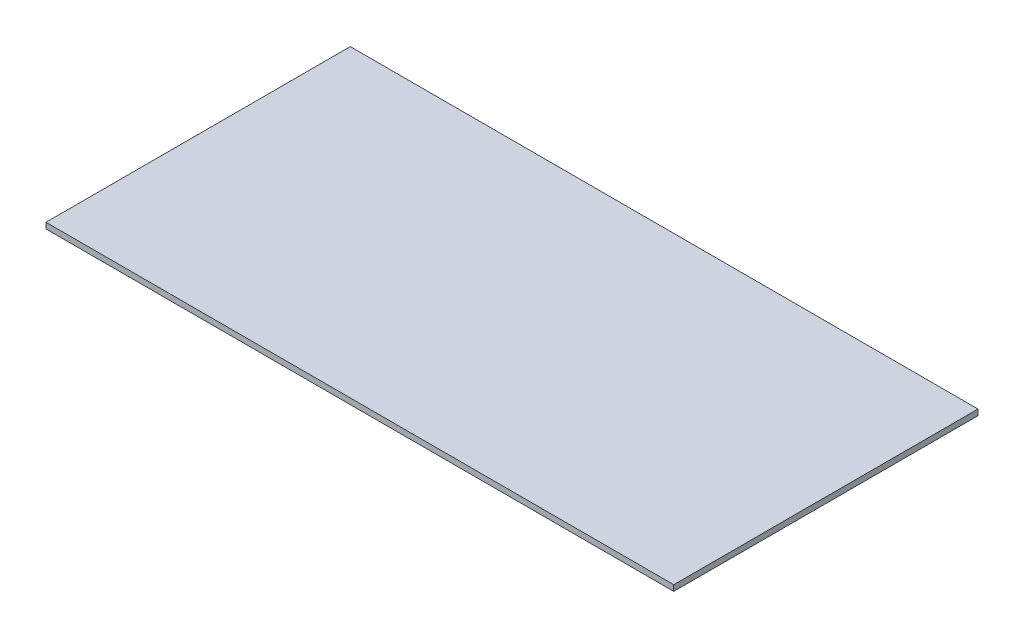
SolidWorks part; units mm, degrees
ref_plane "Front Plane" through (0, 0, 0) normal (0, 0, 1) x (1, 0, 0)
ref_plane "Top Plane" through (0, 0, 0) normal (0, 1, 0) x (1, 0, 0)
ref_plane "Right Plane" through (0, 0, 0) normal (1, 0, 0) x (0, 0, -1)
sketch "Sketch1" plane through (0, 0, 0) normal (0, 1, 0) x (1, 0, 0)
  line L1 (-65.5079, -31.75) -> (65.5079, -31.75)
  line L2 (-65.5079, -31.75) -> (-65.5079, 31.75)
  line L3 (-65.5079, 31.75) -> (65.5079, 31.75)
  line L4 (65.5079, -31.75) -> (65.5079, 31.75)
  line L5 (-65.5079, -31.75) -> (65.5079, 31.75) construction
  line L6 (-65.5079, 31.75) -> (65.5079, -31.75) construction
  point P0 (0, 0)
  dimension "D1" = 131.0157
  dimension "D2" = 63.5
extrude "Boss-Extrude1" add sketch "Sketch1" along normal blind 1.2141
